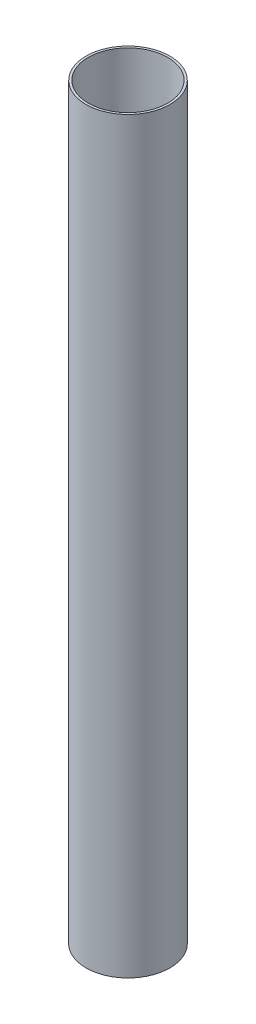
SolidWorks part; units mm, degrees
ref_plane "Front Plane" through (0, 0, 0) normal (0, 0, 1) x (1, 0, 0)
ref_plane "Top Plane" through (0, 0, 0) normal (0, 1, 0) x (1, 0, 0)
ref_plane "Right Plane" through (0, 0, 0) normal (1, 0, 0) x (0, 0, -1)
sketch "Sketch1" plane through (0, 0, 0) normal (0, 0, 1) x (1, 0, 0)
  line L1 (26.9748, 508) -> (28.4988, 508)
  line L2 (26.9748, 508) -> (26.9748, 0)
  line L3 (26.9748, 0) -> (28.4988, 0)
  line L4 (28.4988, 508) -> (28.4988, 0)
  dimension "D1" = 0
  dimension "D2" = 26.9748
  dimension "D3" = 1.524
  dimension "D4" = 508
ref_axis "Central Axis" through (0, 797.9133, 0) along (0, -1, 0)
revolve "Revolve1" add sketch "Sketch1" angle 360 about axis through (0, 797.9133, 0) along (0, -1, 0)
